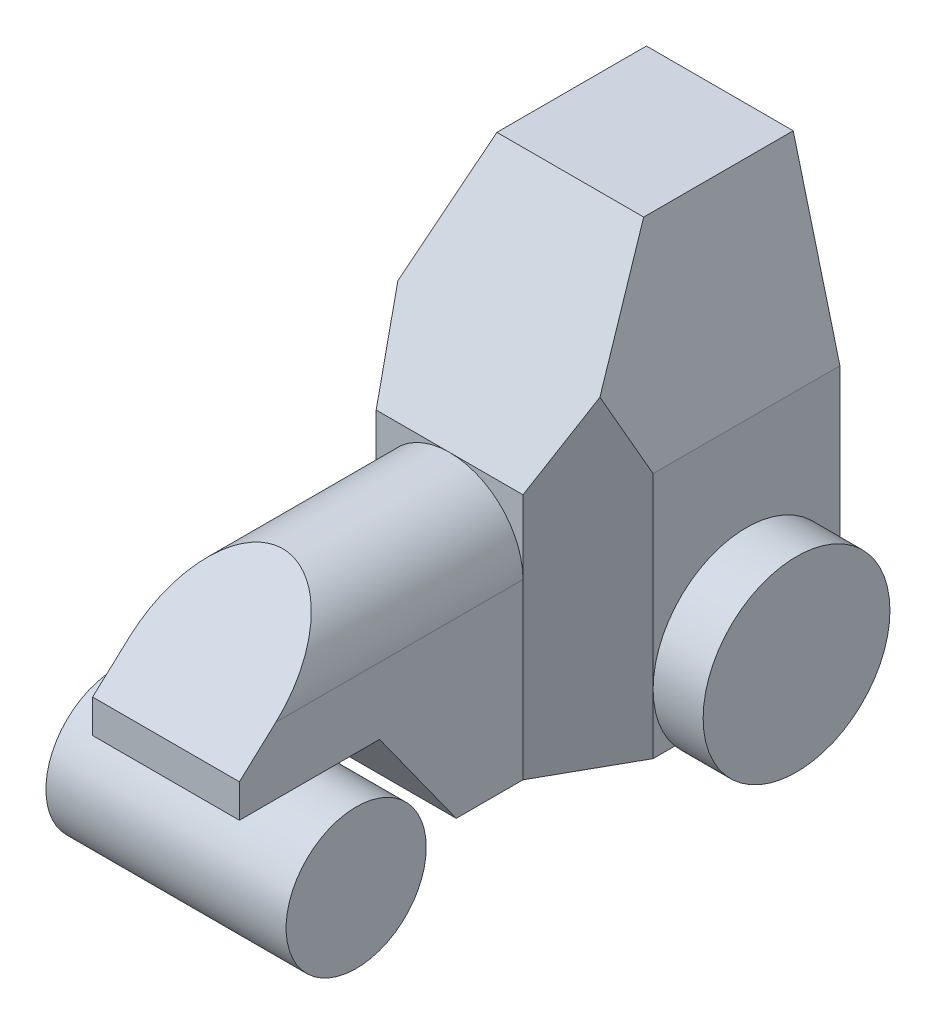
SolidWorks part; units mm, degrees
ref_plane "Front Plane" through (0, 0, 0) normal (0, 0, 1) x (1, 0, 0)
ref_plane "Top Plane" through (0, 0, 0) normal (0, 1, 0) x (1, 0, 0)
ref_plane "Right Plane" through (0, 0, 0) normal (1, 0, 0) x (0, 0, -1)
sketch "Sketch1" plane through (0, 0, 0) normal (0, 1, 0) x (1, 0, 0)
  line L1 (0, 0) -> (72, 0)
  line L2 (0, 0) -> (0, 81)
  line L3 (0, 81) -> (72, 81)
  line L4 (72, 0) -> (72, 81)
  dimension "D1" = 72
  dimension "D2" = 81
extrude "Boss-Extrude1" add sketch "Sketch1" along normal blind 128
sketch "Sketch2" plane through (0, 128, 0) normal (0, 1, 0) x (1, 0, 0)
  line L0 (36, 0) -> (36, 81) construction
  line L1 (0, 0) -> (72, 0) construction
  line L2 (72, 81) -> (0, 81) construction
  line L3 (72, 25) -> (58, 0)
  line L4 (72, 0) -> (72, 81) construction
  line L5 (58, 0) -> (72, 0)
  line L6 (72, 0) -> (72, 25)
  line L7 (14, 0) -> (0, 0)
  line L8 (0, 0) -> (0, 25)
  line L9 (0, 25) -> (14, 0)
  dimension "D1" = 14
  dimension "D2" = 25
extrude "Cut-Extrude1" cut sketch "Sketch2" against normal through all
sketch "Sketch3" plane through (0, 0, 0) normal (0, 0, 1) x (1, 0, 0)
  line L0 (36, 128) -> (36, 0) construction
  line L1 (14, 128) -> (58, 128) construction
  line L2 (14, 0) -> (58, 0) construction
  line L3 (58, 128) -> (72, 74)
  line L4 (72, 0) -> (72, 128) construction
  line L5 (72, 74) -> (72, 128)
  line L6 (72, 128) -> (58, 128)
  line L7 (14, 128) -> (0, 74)
  line L8 (0, 74) -> (0, 128)
  line L9 (0, 128) -> (14, 128)
  dimension "D1" = 54
  dimension "D2" = 14
extrude "Cut-Extrude2" cut sketch "Sketch3" against normal through all
sketch "Sketch4" plane through (72, 0, 0) normal (1, 0, 0) x (0, 0, -1)
  line L0 (0, 74) -> (36.1801, 128)
  line L1 (0, 0) -> (0, 128) construction
  line L2 (81, 128) -> (0, 128) construction
  line L3 (36.1801, 128) -> (0, 128)
  line L4 (0, 128) -> (0, 74)
  line L5 (25, 74) -> (0, 74) construction
  dimension "D1" = 65
extrude "Cut-Extrude3" cut sketch "Sketch4" against normal blind 128
sketch "Sketch5" plane through (72, 0, 0) normal (1, 0, 0) x (0, 0, -1)
  line L0 (25, 0) -> (81, 0) construction
  line L1 (81, 74) -> (81, 0) construction
  circle A0 centre (53, 18) radius 28
  dimension "D1" = 56
  dimension "D2" = 18
extrude "Boss-Extrude2" add sketch "Sketch5" along normal blind 15
sketch "Sketch6" plane through (0, 0, 0) normal (-1, 0, 0) x (0, 0, 1)
  circle A0 centre (-53, 18) radius 28
  dimension "D1" = 56
extrude "Boss-Extrude3" add sketch "Sketch6" along normal blind 15
sketch "Sketch8" plane through (0, 0, 0) normal (0, 0, 1) x (1, 0, 0)
  line L0 (36, 74) -> (36, 0) construction
  line L1 (14, 74) -> (58, 74) construction
  line L2 (14, 0) -> (58, 0) construction
  line L3 (58, 0) -> (58, 74) construction
  line L4 (14, 52) -> (58, 52) construction
  line L5 (14, 52) -> (14, 0)
  line L6 (14, 0) -> (58, 0)
  line L7 (58, 0) -> (58, 52)
  arc A0 (58, 52) -> (14, 52) centre (36, 52) ccw
extrude "Boss-Extrude4" add sketch "Sketch8" along normal blind 85
sketch "Sketch9" plane through (58, 0, 0) normal (1, 0, 0) x (0, 0, -1)
  line L0 (-85, 32) -> (-43, 32)
  line L1 (-85, 0) -> (-85, 52) construction
  line L2 (-43, 32) -> (-20, 0)
  line L3 (-85, 0) -> (0, 0) construction
  line L4 (-20, 0) -> (-85, 0)
  line L5 (-85, 0) -> (-85, 32)
  line L6 (-85, 42) -> (-50, 74)
  line L7 (-50, 74) -> (-85, 74)
  line L8 (-85, 74) -> (-85, 42)
  dimension "D1" = 42
  dimension "D2" = 65
  dimension "D3" = 32
  dimension "D4" = 10
  dimension "D5" = 35
extrude "Cut-Extrude4" cut sketch "Sketch9" against normal blind 85
sketch "Sketch10" plane through (72, 0, 0) normal (1, 0, 0) x (0, 0, -1)
  line L0 (53, -10) -> (-85, -10) construction
  line L1 (-85, 32) -> (-85, -10) construction
  circle A0 centre (-64, 11) radius 21
  circle A1 centre (53, 18) radius 28 construction
  dimension "D1" = 42
extrude "Boss-Extrude5" add sketch "Sketch10" against normal blind 72 separate body
